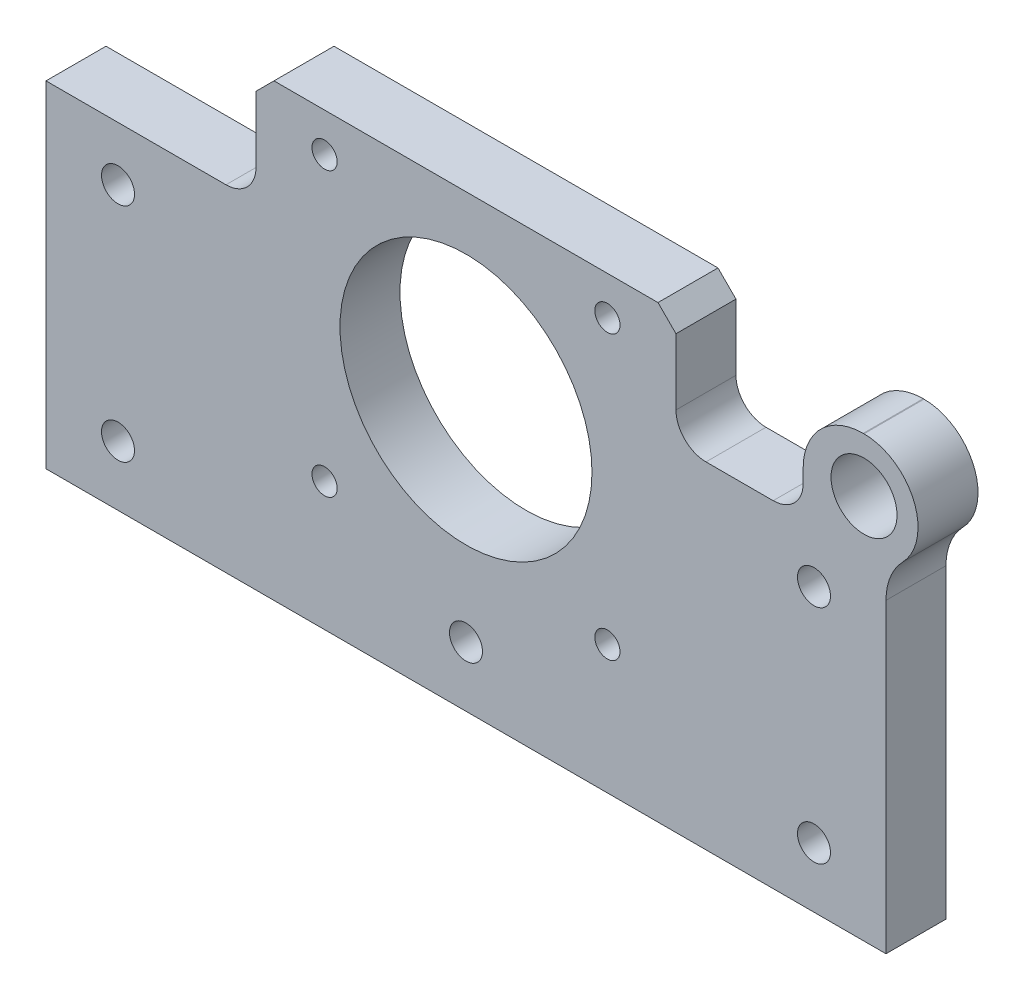
SolidWorks part; units mm, degrees
material "1023 Листовая углеродистая сталь (SS)"
ref_plane "Front" through (0, 0, 0) normal (0, 0, 1) x (1, 0, 0)
ref_plane "Top" through (0, 0, 0) normal (0, 1, 0) x (1, 0, 0)
ref_plane "Right" through (0, 0, 0) normal (1, 0, 0) x (0, 0, -1)
sketch "Sketch1" plane through (0, 0, 0) normal (0, 0, 1) x (1, 0, 0)
  line L0 (35, 56) -> (70, 56)
  line L1 (-70, 56) -> (-35, 56)
  line L2 (-70, 56) -> (-70, 0)
  line L3 (-70, 0) -> (70, 0)
  line L4 (70, 56) -> (70, 0)
  line L5 (-35, 75) -> (35, 75)
  line L6 (-35, 75) -> (-35, 56)
  line L8 (35, 75) -> (35, 56)
  dimension "D1" = 56
  dimension "D2" = 140
  dimension "D3" = 75
  dimension "D4" = 70
extrude "Extrude1" add sketch "Sketch1" along normal blind 10
hole_wizard "M5 Tapped Hole1" positions "Sketch2" profile "Sketch3" tap size "M5" standard "DIN" end condition through all
sketch "Sketch2" plane through (0, 0, 0) normal (0, 0, -1) x (-1, 0, 0)
  line L1 (-23.57, 68.57) -> (23.57, 68.57)
  line L2 (-23.57, 68.57) -> (-23.57, 21.43)
  line L3 (-23.57, 21.43) -> (23.57, 21.43)
  line L4 (23.57, 68.57) -> (23.57, 21.43)
  line L5 (0, 21.43) -> (0, 0) construction
  point P0 (-23.57, 68.57)
  point P3 (23.57, 68.57)
  point P6 (-23.57, 21.43)
  point P9 (23.57, 21.43)
sketch "Sketch3" plane through (23.57, 68.57, 0) normal (1, 0, 0) x (0, 1, 0)
  line L0 (0, 0) -> (0, 10)
  line L1 (0, 10) -> (2.1, 10)
  line L2 (2.1, 10) -> (2.1, 0)
  line L5 (2.1, 0) -> (0, 0)
  line L11 (0, -6.35) -> (0, 107.95) construction
  dimension "Диаметр проходного сверла" = 4.2
  dimension "Глубина проходного сверла" = 10
cosmetic thread "Cosmetic Thread1" parameters "D2"=5
cosmetic thread "Cosmetic Thread2" parameters "D2"=5
cosmetic thread "Cosmetic Thread3" parameters "D2"=5
cosmetic thread "Cosmetic Thread4" parameters "D2"=5
sketch "Sketch4" plane through (0, 0, 10) normal (0, 0, 1) x (1, 0, 0)
  line L0 (0, 45) -> (0, 0) construction
  circle A0 centre (0, 45) radius 21
  dimension "D1" = 42
  dimension "D2" = 45
extrude "Cut-Extrude1" cut sketch "Sketch4" against normal up to next
chamfer "Chamfer1" distance 3 angle 45 2 edges at (-35, 75, 5) (35, 75, 5)
hole_wizard "CBORE for M5 Hex Socket Head Cap Screw1" positions "Sketch5" profile "Sketch6" counterbore size "M5" standard "DIN" end condition through all
sketch "Sketch5" plane through (0, 0, 0) normal (0, 0, -1) x (-1, 0, 0)
  line L0 (-70, 0) -> (-70, 56) construction
  line L1 (-70, 56) -> (-35, 56) construction
  line L2 (70, 0) -> (-70, 0) construction
  line L3 (70, 56) -> (70, 0) construction
  line L4 (35, 56) -> (70, 56) construction
  point P0 (-58, 10)
  point P2 (0, 10)
  point P4 (58, 10)
  point P6 (58, 47)
  point P8 (-58, 47)
  point P22 (52.5, 56)
  dimension "D1" = 12
  dimension "D2" = 9
  dimension "D3" = 12
  dimension "D4" = 10
  dimension "D5" = 12
  dimension "D6" = 12
  dimension "D7" = 10
  dimension "D8" = 9
  dimension "D9" = 10
sketch "Sketch6" plane through (58, 10, 0) normal (1, 0, 0) x (0, 1, 0)
  line L0 (0, 0) -> (0, 10)
  line L1 (0, 10) -> (2.75, 10)
  line L3 (2.75, 10) -> (2.75, 5.4)
  line L4 (2.75, 5.4) -> (5, 5.4)
  line L5 (5, 5.4) -> (5, 0)
  line L7 (5, 0) -> (0, 0)
  line L11 (0, -6.35) -> (0, 107.95) construction
  dimension "Диаметр сквозного отверстия" = 5.5
  dimension "Глубина сквозного отверстия" = 10
  dimension "Диаметр цековки" = 10
  dimension "Глубина цековки" = 5.4
sketch "Sketch7" plane through (0, 0, 0) normal (0, 0, -1) x (-1, 0, 0)
  line L0 (-66.3416, 73.2229) -> (-56.1976, 73.2229)
  line L1 (-70, 56) -> (-56.1976, 56)
  line L4 (-56.1976, 56) -> (-56.1976, 73.2229)
  line L5 (-70, 56) -> (-35, 56) construction
  arc A0 (-66.3416, 73.2229) -> (-70, 56) centre (-66.3416, 64.2229) ccw
  circle A1 centre (-66.3416, 64.2229) radius 6 construction
  dimension "D3" = 18
  dimension "D4" = 12
extrude "Extrude2" add sketch "Sketch7" against normal up to surface (10 mm away) up to face at (55.25, 10, 10)
fillet "Fillet3" radius 10 2 edges at (56.1976, 73.2229, 5) (70, 56, 5)
fillet "Fillet4" radius 5 3 edges at (56.1976, 56, 5) (35, 56, 5) (-35, 56, 5)
hole_wizard "M12x1.0 Tapped Hole2" positions "Sketch10" profile "Sketch11" tap size "M12x1.0" standard "DIN" end condition through all
sketch "Sketch10" plane through (0, 0, 0) normal (0, 0, -1) x (-1, 0, 0)
  point P0 (-66.3416, 64.2229)
sketch "Sketch11" plane through (66.3416, 64.2229, 0) normal (1, 0, 0) x (0, 1, 0)
  line L0 (0, 0) -> (0, 10)
  line L1 (0, 10) -> (5.5, 10)
  line L2 (5.5, 10) -> (5.5, 0)
  line L5 (5.5, 0) -> (0, 0)
  line L11 (0, -6.35) -> (0, 107.95) construction
  dimension "Диаметр проходного сверла" = 11
  dimension "Глубина проходного сверла" = 10
cosmetic thread "Cosmetic Thread7" parameters "D2"=12
hole_wizard "M12x1.0 Tapped Hole1" positions "Sketch8" profile "Sketch9" tap size "M12x1.0" standard "DIN" end condition through all
sketch "Sketch8" plane through (0, 0, 0) normal (0, 0, -1) x (-1, 0, 0)
  point P0 (-66.3416, 64.2229)
sketch "Sketch9" plane through (66.3416, 64.2229, 0) normal (1, 0, 0) x (0, 1, 0)
  line L0 (0, 0) -> (0, 10)
  line L1 (0, 10) -> (5.5, 10)
  line L2 (5.5, 10) -> (5.5, 0)
  line L5 (5.5, 0) -> (0, 0)
  line L11 (0, -6.35) -> (0, 107.95) construction
  dimension "Диаметр проходного сверла" = 11
  dimension "Глубина проходного сверла" = 10
